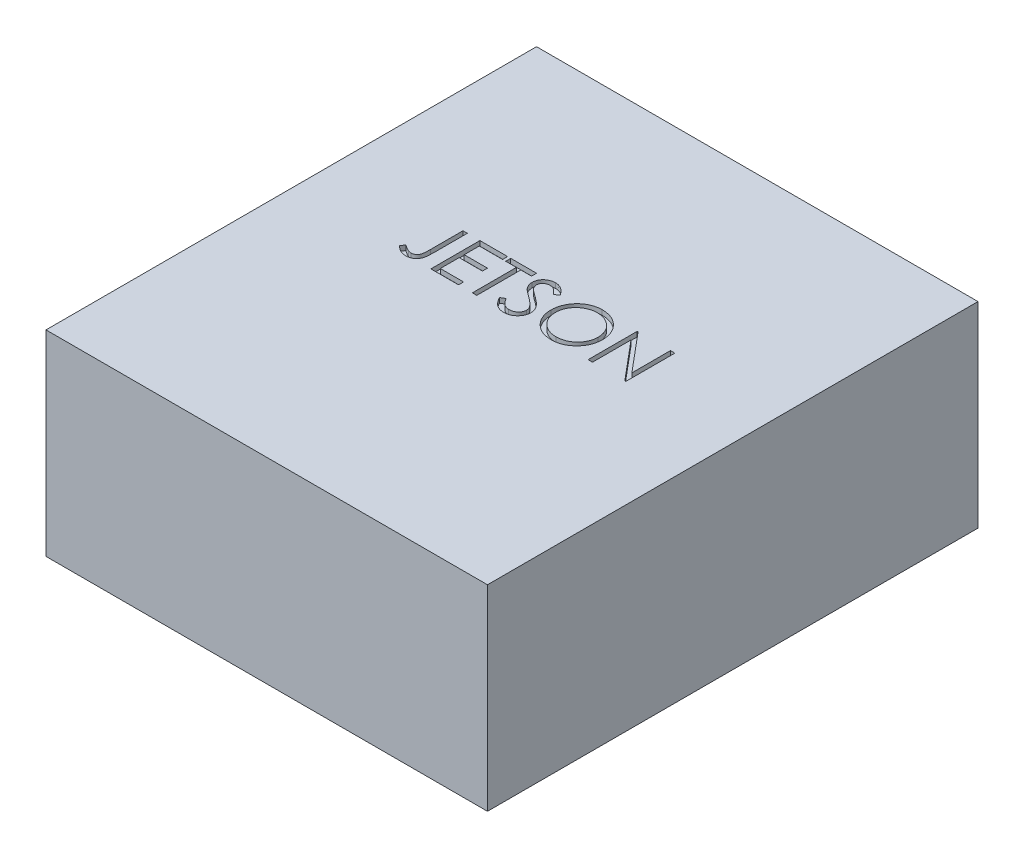
SolidWorks part; units mm, degrees
ref_plane "Front Plane" through (0, 0, 0) normal (0, 0, 1) x (1, 0, 0)
ref_plane "Top Plane" through (0, 0, 0) normal (0, 1, 0) x (1, 0, 0)
ref_plane "Right Plane" through (0, 0, 0) normal (1, 0, 0) x (0, 0, -1)
sketch "Sketch1" plane through (0, 0, 0) normal (0, 1, 0) x (1, 0, 0)
  line L1 (0, 0) -> (90, 0)
  line L2 (0, 0) -> (0, 100)
  line L3 (0, 100) -> (90, 100)
  line L4 (90, 0) -> (90, 100)
  dimension "D1" = 100
  dimension "D2" = 90
extrude "Boss-Extrude1" add sketch "Sketch1" along normal blind 40
sketch "Sketch2" plane through (0, 40, 0) normal (0, 1, 0) x (1, 0, 0)
  line L0 (0, 50) -> (90, 50) construction
  line L1 (0, 100) -> (0, 0) construction
  line L2 (90, 0) -> (90, 100) construction
  text T0 "JETSON" font "Century Gothic" height 10
extrude "Cut-Extrude1" cut sketch "Sketch2" against normal blind 1
